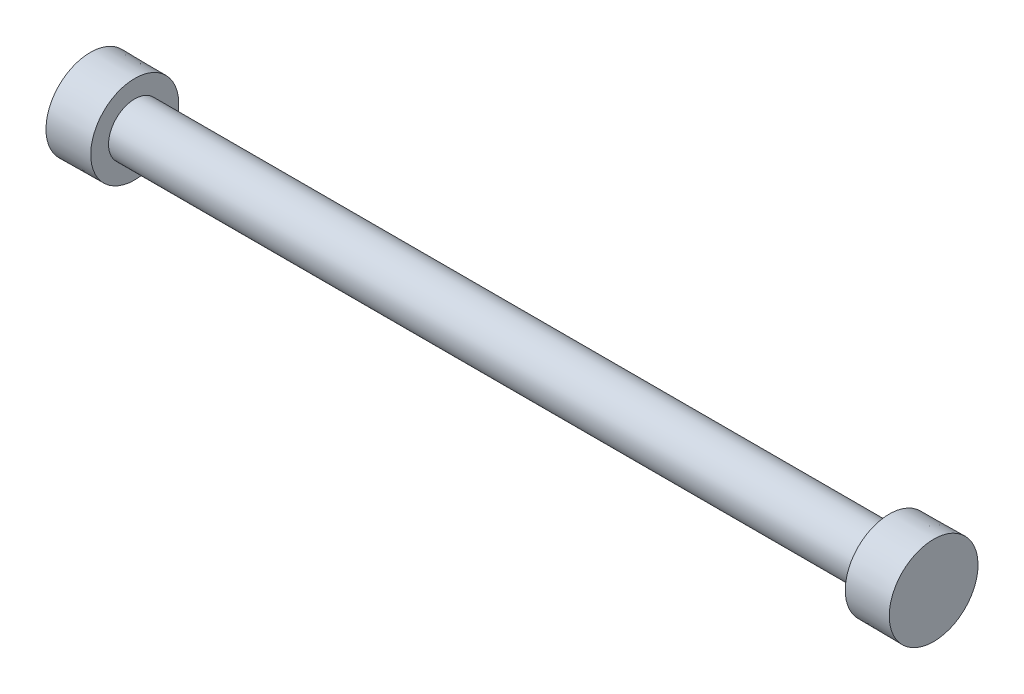
SolidWorks part; units mm, degrees
ref_plane "Front Plane" through (0, 0, 0) normal (0, 0, 1) x (1, 0, 0)
ref_plane "Top Plane" through (0, 0, 0) normal (0, 1, 0) x (1, 0, 0)
ref_plane "Right Plane" through (0, 0, 0) normal (1, 0, 0) x (0, 0, -1)
sketch "Sketch1" plane through (0, 0, 0) normal (0, 0, 1) x (1, 0, 0)
  line L0 (-33.1144, 0.5332) -> (61.8852, 0.5332) construction
  line L1 (-33.1144, 0.5332) -> (-33.1144, 5.5332)
  line L2 (-33.1144, 5.5332) -> (-28.1146, 5.4896)
  line L3 (-28.1146, 5.4896) -> (-28.1146, 3.4896)
  line L4 (-28.1146, 3.4896) -> (56.8854, 3.4896)
  line L5 (56.8854, 3.4896) -> (56.8854, 5.4896)
  line L6 (56.8854, 5.4896) -> (61.8852, 5.5332)
  line L7 (61.8852, 5.5332) -> (61.8852, 0.5332)
  line L8 (-33.1144, 0.5332) -> (61.8852, 0.5332)
  dimension "D1" = 85
  dimension "D2" = 5
  dimension "D3" = 5
  dimension "D4" = 5
revolve "Revolve1" add sketch "Sketch1" angle 360 about L8
